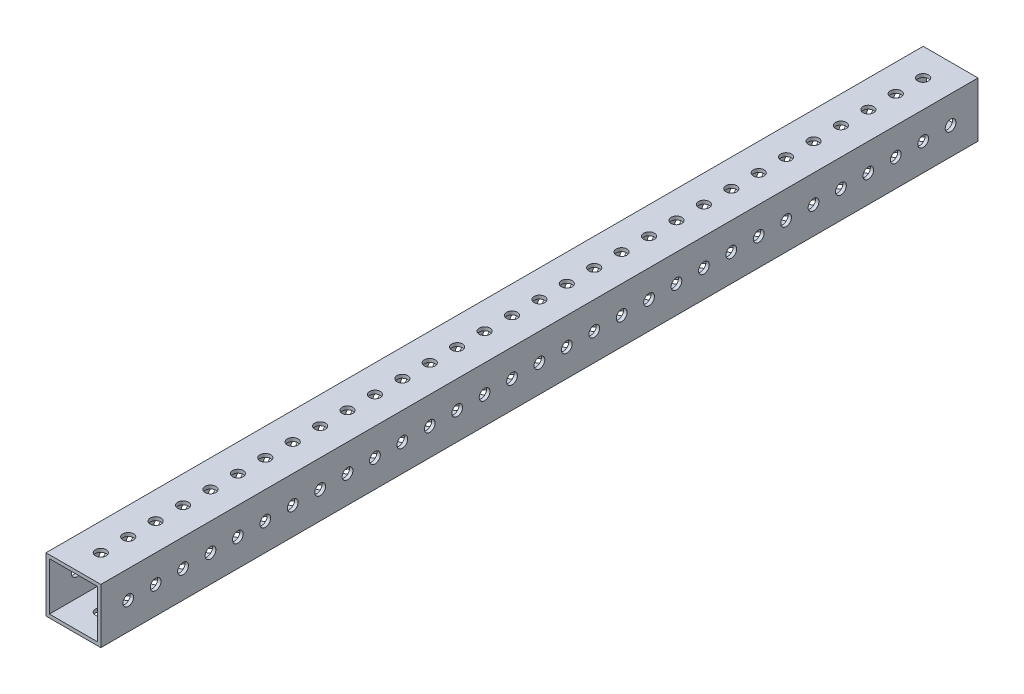
SolidWorks part; units mm, degrees
material "6061 Alloy"
ref_plane "Front Plane" through (0, 0, 0) normal (0, 0, 1) x (1, 0, 0)
ref_plane "Top Plane" through (0, 0, 0) normal (0, 1, 0) x (1, 0, 0)
ref_plane "Right Plane" through (0, 0, 0) normal (1, 0, 0) x (0, 0, -1)
sketch "Sketch1" plane through (0, 0, 0) normal (0, 0, 1) x (1, 0, 0)
  line L0 (1.5875, 1.5875) -> (23.8125, 1.5875)
  line L1 (0, 0) -> (25.4, 0)
  line L2 (0, 0) -> (0, 25.4)
  line L3 (0, 25.4) -> (25.4, 25.4)
  line L4 (25.4, 0) -> (25.4, 25.4)
  line L5 (23.8125, 1.5875) -> (23.8125, 23.8125)
  line L6 (1.5875, 23.8125) -> (23.8125, 23.8125)
  line L7 (1.5875, 1.5875) -> (1.5875, 23.8125)
  dimension "D1" = 25.4
  dimension "D2" = 1.5875
extrude "Boss-Extrude1" add sketch "Sketch1" along normal blind 406.4
sketch "Sketch2" plane through (25.4, 0, 0) normal (1, 0, 0) x (0, 0, -1)
  line L0 (-406.4, 0) -> (-406.4, 25.4) construction
  line L1 (-393.7, 12.7) -> (-381, 12.7) construction
  circle A0 centre (-393.7, 12.7) radius 2.4892
  circle A1 centre (-381, 12.7) radius 2.4892
  circle A2 centre (-368.3, 12.7) radius 2.4892
  circle A3 centre (-355.6, 12.7) radius 2.4892
  circle A4 centre (-342.9, 12.7) radius 2.4892
  circle A5 centre (-330.2, 12.7) radius 2.4892
  circle A6 centre (-317.5, 12.7) radius 2.4892
  circle A7 centre (-304.8, 12.7) radius 2.4892
  circle A8 centre (-292.1, 12.7) radius 2.4892
  circle A9 centre (-279.4, 12.7) radius 2.4892
  circle A10 centre (-266.7, 12.7) radius 2.4892
  circle A11 centre (-254, 12.7) radius 2.4892
  circle A12 centre (-241.3, 12.7) radius 2.4892
  circle A13 centre (-228.6, 12.7) radius 2.4892
  circle A14 centre (-215.9, 12.7) radius 2.4892
  circle A15 centre (-203.2, 12.7) radius 2.4892
  circle A16 centre (-190.5, 12.7) radius 2.4892
  circle A17 centre (-177.8, 12.7) radius 2.4892
  circle A18 centre (-165.1, 12.7) radius 2.4892
  circle A19 centre (-152.4, 12.7) radius 2.4892
  circle A20 centre (-139.7, 12.7) radius 2.4892
  circle A21 centre (-127, 12.7) radius 2.4892
  circle A22 centre (-114.3, 12.7) radius 2.4892
  circle A23 centre (-101.6, 12.7) radius 2.4892
  circle A24 centre (-88.9, 12.7) radius 2.4892
  circle A25 centre (-76.2, 12.7) radius 2.4892
  circle A26 centre (-63.5, 12.7) radius 2.4892
  circle A27 centre (-50.8, 12.7) radius 2.4892
  circle A28 centre (-38.1, 12.7) radius 2.4892
  circle A29 centre (-25.4, 12.7) radius 2.4892
  circle A30 centre (-12.7, 12.7) radius 2.4892
  point P4 (-406.4, 12.7)
  dimension "D1" = 4.9784
  dimension "D2" = 12.7
  dimension "D4" = 12.7
  dimension "D3" = 31
extrude "Cut-Extrude1" cut sketch "Sketch2" against normal through all
sketch "Sketch4" plane through (0, 25.4, 0) normal (0, 1, 0) x (1, 0, 0)
  line L0 (25.4, 0) -> (0, 0) construction
  line L1 (12.7, -12.7) -> (12.7, -25.4) construction
  circle A0 centre (12.7, -12.7) radius 2.4892
  circle A1 centre (12.7, -25.4) radius 2.4892
  circle A2 centre (12.7, -38.1) radius 2.4892
  circle A3 centre (12.7, -50.8) radius 2.4892
  circle A4 centre (12.7, -63.5) radius 2.4892
  circle A5 centre (12.7, -76.2) radius 2.4892
  circle A6 centre (12.7, -88.9) radius 2.4892
  circle A7 centre (12.7, -101.6) radius 2.4892
  circle A8 centre (12.7, -114.3) radius 2.4892
  circle A9 centre (12.7, -127) radius 2.4892
  circle A10 centre (12.7, -139.7) radius 2.4892
  circle A11 centre (12.7, -152.4) radius 2.4892
  circle A12 centre (12.7, -165.1) radius 2.4892
  circle A13 centre (12.7, -177.8) radius 2.4892
  circle A14 centre (12.7, -190.5) radius 2.4892
  circle A15 centre (12.7, -203.2) radius 2.4892
  circle A16 centre (12.7, -215.9) radius 2.4892
  circle A17 centre (12.7, -228.6) radius 2.4892
  circle A18 centre (12.7, -241.3) radius 2.4892
  circle A19 centre (12.7, -254) radius 2.4892
  circle A20 centre (12.7, -266.7) radius 2.4892
  circle A21 centre (12.7, -279.4) radius 2.4892
  circle A22 centre (12.7, -292.1) radius 2.4892
  circle A23 centre (12.7, -304.8) radius 2.4892
  circle A24 centre (12.7, -317.5) radius 2.4892
  circle A25 centre (12.7, -330.2) radius 2.4892
  circle A26 centre (12.7, -342.9) radius 2.4892
  circle A27 centre (12.7, -355.6) radius 2.4892
  circle A28 centre (12.7, -368.3) radius 2.4892
  circle A29 centre (12.7, -381) radius 2.4892
  circle A30 centre (12.7, -393.7) radius 2.4892
  point P5 (12.7, 0)
  dimension "D1" = 4.9784
  dimension "D2" = 12.7
  dimension "D4" = 12.7
  dimension "D3" = 31
extrude "Cut-Extrude2" cut sketch "Sketch4" against normal through all
